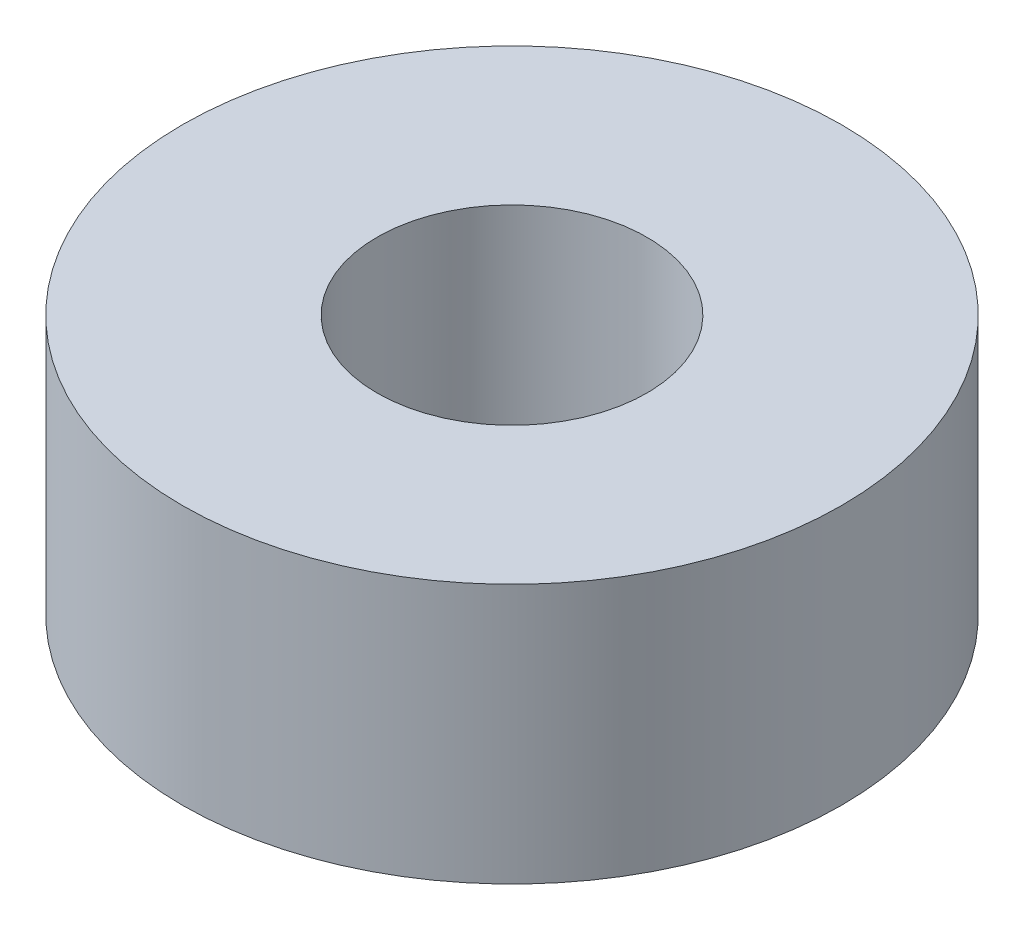
SolidWorks part; units mm, degrees
ref_plane "Front Plane" through (0, 0, 0) normal (0, 0, 1) x (1, 0, 0)
ref_plane "Top Plane" through (0, 0, 0) normal (0, 1, 0) x (1, 0, 0)
ref_plane "Right Plane" through (0, 0, 0) normal (1, 0, 0) x (0, 0, -1)
sketch "Sketch1" plane through (0, 0, 0) normal (0, 1, 0) x (1, 0, 0)
  circle A0 centre (0, 0) radius 3.302
  circle A1 centre (0, 0) radius 8.0645
  dimension "D1" = 6.604
  dimension "D2" = 4.7625
extrude "Boss-Extrude1" add sketch "Sketch1" along normal mid plane 6.35
